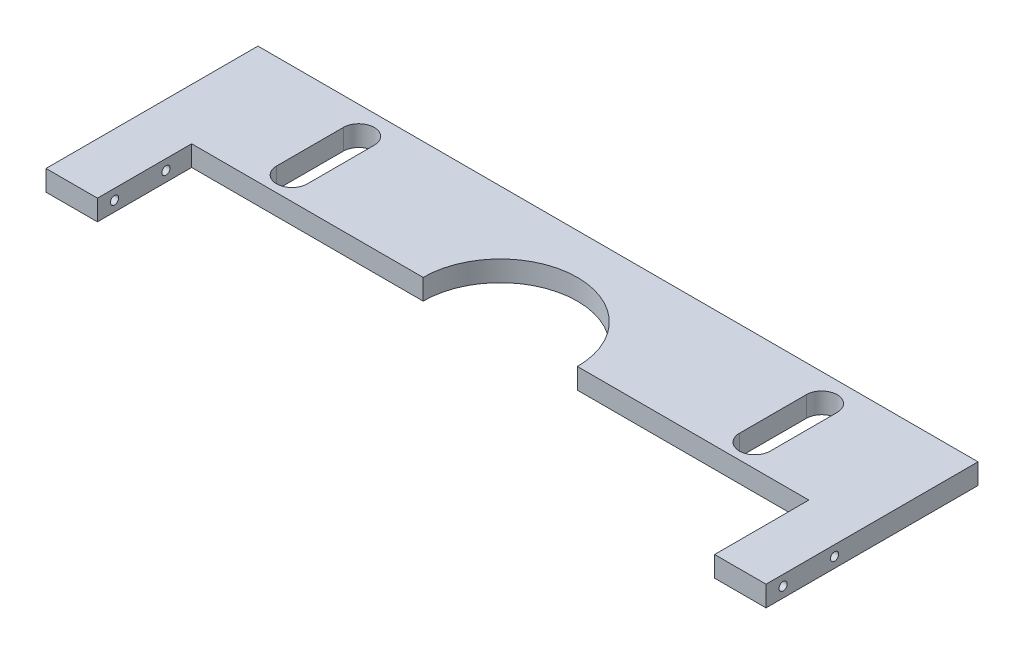
SolidWorks part; units mm, degrees
material "A286 Iron Base Superalloy"
ref_plane "Front Plane" through (0, 0, 0) normal (0, 0, 1) x (1, 0, 0)
ref_plane "Top Plane" through (0, 0, 0) normal (0, 1, 0) x (1, 0, 0)
ref_plane "Right Plane" through (0, 0, 0) normal (1, 0, 0) x (0, 0, -1)
sketch "Sketch2" plane through (0, 0, 0) normal (0, 1, 0) x (1, 0, 0)
  line L1 (-70, -19.445) -> (70, -19.445)
  line L2 (-70, -19.445) -> (-70, 19.445)
  line L3 (-70, 19.445) -> (70, 19.445)
  line L4 (70, -19.445) -> (70, 19.445)
  line L5 (-70, -19.445) -> (70, 19.445) construction
  line L6 (-70, 19.445) -> (70, -19.445) construction
  point P0 (0, 0)
  dimension "D1" = 140
  dimension "D2" = 38.89
extrude "Boss-Extrude1" add sketch "Sketch2" along normal blind 4
sketch "Sketch3" plane through (-70, 0, 0) normal (-1, 0, 0) x (0, 0, 1)
  line L0 (-19.445, 4) -> (19.445, 4) construction
  line L1 (-19.445, 0) -> (19.445, 0) construction
  line L2 (0, 0) -> (0, 4) construction
  line L3 (19.445, 4) -> (19.445, 0) construction
  circle A0 centre (4.445, 2) radius 1.5
  circle A1 centre (14.445, 2) radius 1.5
  dimension "D1" = 2
  dimension "D2" = 5
  dimension "D3" = 10
hole_wizard "M2x0.4 Tapped Hole1" positions "Sketch5" profile "Sketch4" tap size "M2x0.4" standard "ANSI Metric"
sketch "Sketch5" plane through (-70, 0, 0) normal (-1, 0, 0) x (0, 0, 1)
  point P0 (4.445, 2)
  point P3 (14.445, 2)
sketch "Sketch4" plane through (-70, 2, 4.445) normal (0, 1, 0) x (0, 0, 1)
  line L0 (0, 0) -> (0, 18.4807)
  line L1 (0, 18.4807) -> (0.8, 18)
  line L2 (0.8, 18) -> (0.8, 0)
  line L5 (0.8, 0) -> (0, 0)
  line L10 (0, 18.4807) -> (-0.8, 18) construction
  line L11 (0, -6.35) -> (0, 107.95) construction
  dimension "Tap Drill Dia." = 1.6
  dimension "Tap Drill Depth" = 18
  dimension "Drill Angle" = 118
cosmetic thread "Hole Thread1" parameters "D1"=4, "D2"=2
cosmetic thread "Hole Thread2" parameters "D1"=4, "D2"=2
mirror "Mirror1" about plane through (0, 0, 0) normal (1, 0, 0) of "M2x0.4 Tapped Hole1"
sketch "Sketch6" plane through (0, 4, 0) normal (0, 1, 0) x (1, 0, 0)
  line L1 (-70, -19.445) -> (70, -19.445) construction
  line L2 (-60, -19.445) -> (60, -19.445)
  line L3 (-60, -19.445) -> (-60, 0.555)
  line L4 (-60, 0.555) -> (60, 0.555)
  line L5 (60, -19.445) -> (60, 0.555)
  dimension "D1" = 20
  dimension "D2" = 120
  dimension "D3" = 60
extrude "Cut-Extrude1" cut sketch "Sketch6" against normal through all
sketch "Sketch8" plane through (0, 4, 0) normal (0, 1, 0) x (1, 0, 0)
  line L1 (-70, -19.445) -> (-35, -19.445)
  line L2 (-70, -19.445) -> (-70, -21.735)
  line L3 (-70, -21.735) -> (-35, -21.735)
  line L4 (-35, -19.445) -> (-35, -21.735)
  line L5 (60, -19.445) -> (70, -19.445)
  line L6 (60, -19.445) -> (60, -21.735)
  line L7 (60, -21.735) -> (70, -21.735)
  line L8 (70, -19.445) -> (70, -21.735)
  dimension "D1" = 2.29
  dimension "D2" = 2.29
extrude "Boss-Extrude2" add sketch "Sketch8" against normal through all
sketch "Sketch9" plane through (0, 4, 0) normal (0, 1, 0) x (1, 0, 0)
  line L1 (-60, -19.445) -> (-35, -19.445)
  line L2 (-60, -19.445) -> (-60, -21.735)
  line L3 (-60, -21.735) -> (-35, -21.735)
  line L4 (-35, -19.445) -> (-35, -21.735)
extrude "Cut-Extrude3" cut sketch "Sketch9" against normal through all
sketch "Sketch10" plane through (0, 4, 0) normal (0, 1, 0) x (1, 0, 0)
  line L1 (-70, 19.445) -> (70, 19.445)
  line L2 (-70, 19.445) -> (-70, 23.445)
  line L3 (-70, 23.445) -> (70, 23.445)
  line L4 (70, 19.445) -> (70, 23.445)
  dimension "D1" = 4
extrude "Boss-Extrude3" add sketch "Sketch10" against normal through all
sketch "Sketch11" plane through (0, 4, 0) normal (0, 1, 0) x (1, 0, 0)
  line L0 (70, -21.735) -> (70, 23.445) construction
  line L1 (-70, -21.735) -> (70, -21.735)
  line L2 (-70, -21.735) -> (-70, -17.765)
  line L3 (-70, -17.765) -> (70, -17.765)
  line L4 (70, -21.735) -> (70, -17.765)
  dimension "D1" = 3.97
extrude "Cut-Extrude4" cut sketch "Sketch11" against normal blind 10
sketch "Sketch7" plane through (0, 4, 0) normal (0, 1, 0) x (1, 0, 0)
  line L1 (-45, 18.055) -> (-45, 5.055) construction
  line L2 (-42, 18.055) -> (-42, 5.055)
  line L3 (-48, 18.055) -> (-48, 5.055)
  line L4 (45, 18.055) -> (45, 5.055) construction
  line L5 (48, 18.055) -> (48, 5.055)
  line L6 (42, 18.055) -> (42, 5.055)
  line L8 (60, 0.555) -> (-60, 0.555) construction
  arc A2 (-42, 18.055) -> (-48, 18.055) centre (-45, 18.055) ccw
  arc A3 (-48, 5.055) -> (-42, 5.055) centre (-45, 5.055) ccw
  arc A4 (48, 18.055) -> (42, 18.055) centre (45, 18.055) ccw
  arc A5 (42, 5.055) -> (48, 5.055) centre (45, 5.055) ccw
  point P7 (-45, 11.555)
  point P13 (45, 11.555)
  dimension "D1" = 13
  dimension "D2" = 13
  dimension "D4" = 4.5
  dimension "D3" = 4.5
  dimension "D7" = 6
  dimension "D8" = 6
extrude "Cut-Extrude5" cut sketch "Sketch7" against normal through all
sketch "Sketch13" plane through (0, 4, 0) normal (0, 1, 0) x (1, 0, 0)
  line L0 (60, 0.555) -> (-60, 0.555) construction
  line L1 (-15, 0.555) -> (15, 0.555)
  arc A0 (15, 0.555) -> (-15, 0.555) centre (0, 0.555) ccw
  dimension "D1" = 15
extrude "Cut-Extrude6" cut sketch "Sketch13" against normal blind 10
